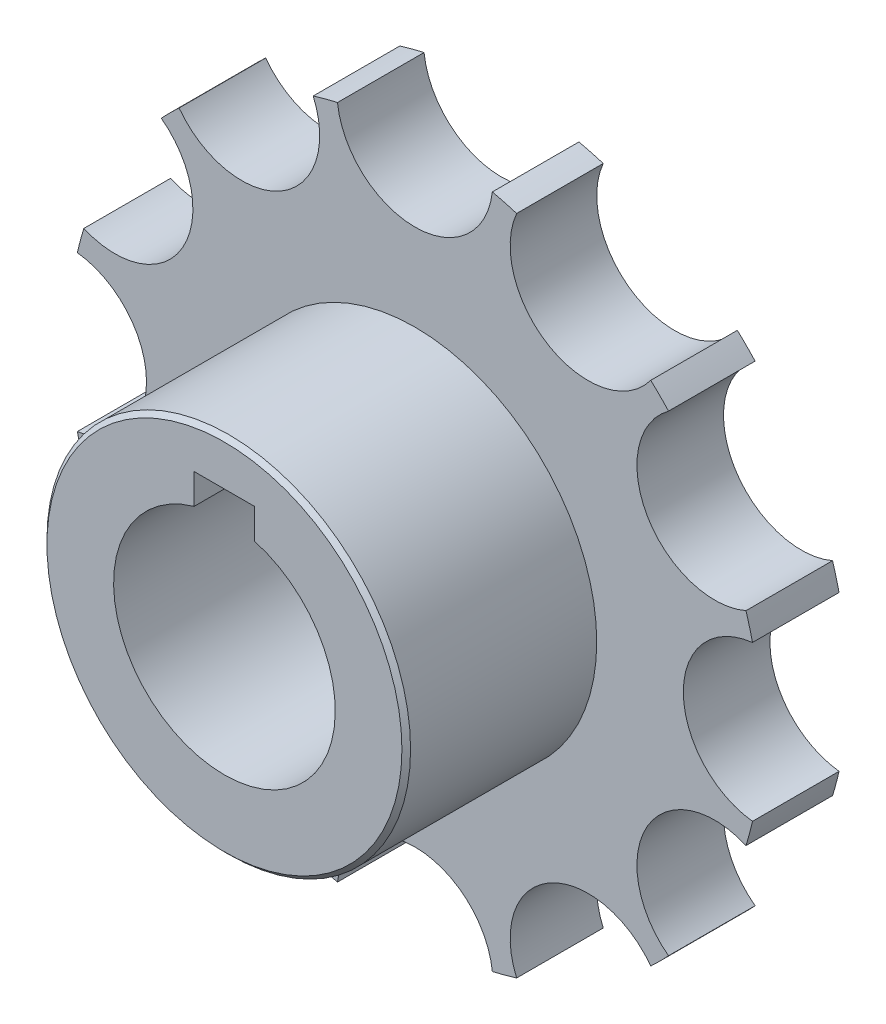
SolidWorks part; units mm, degrees
ref_plane "Přední rovina" through (0, 0, 0) normal (0, 0, 1) x (1, 0, 0)
ref_plane "Horní rovina" through (0, 0, 0) normal (0, 1, 0) x (1, 0, 0)
ref_plane "Pravá rovina" through (0, 0, 0) normal (1, 0, 0) x (0, 0, -1)
sketch "Skica1" plane through (0, 0, 0) normal (0, 0, 1) x (1, 0, 0)
  line L0 (-51.8674, 0) -> (69.1461, 0) construction
  line L1 (0, 65.5579) -> (0, -54.8107) construction
  line L3 (-3.5, 9.8) -> (3.5, 9.8)
  line L4 (-3.5, 9.8) -> (-3.5, 15.8)
  line L5 (-3.5, 15.8) -> (3.5, 15.8)
  line L6 (3.5, 9.8) -> (3.5, 15.8)
  line L7 (-3.5, 9.8) -> (3.5, 15.8) construction
  line L8 (-3.5, 15.8) -> (3.5, 9.8) construction
  circle A0 centre (0, 0) radius 12.8
  circle A1 centre (0, 0) radius 21
  circle A2 centre (0, 0) radius 40
  circle A3 centre (0, 40) radius 9
  circle A4 centre (20, 34.641) radius 9
  circle A5 centre (34.641, 20) radius 9
  circle A6 centre (40, 0) radius 9
  circle A7 centre (34.641, -20) radius 9
  circle A8 centre (20, -34.641) radius 9
  circle A9 centre (0, -40) radius 9
  circle A10 centre (-20, -34.641) radius 9
  circle A11 centre (-34.641, -20) radius 9
  circle A12 centre (-40, 0) radius 9
  circle A13 centre (-34.641, 20) radius 9
  circle A14 centre (-20, 34.641) radius 9
  point P7 (0, 12.8)
  point P41 (0, 0)
  dimension "D1" = 25.6
  dimension "D4" = 42
  dimension "D5" = 80
  dimension "D6" = 18
  dimension "D2" = 3
  dimension "D3" = 7
  dimension "D7" = 12
extrude "Přidat vysunutím2" add sketch "Skica1" along normal blind 10 contours A1 A0 L4 L5 L6 | A14 A2 A13 A12 A11 A10 A9 A8 A7 A6 A5 A4 A3 A1
sketch "Skica2" plane through (0, 0, 10) normal (0, 0, 1) x (1, 0, 0)
  circle A0 centre (0, 0) radius 21
  dimension "D1" = 42
extrude "Přidat vysunutím3" add sketch "Skica2" along normal blind 22
sketch "Skica3" plane through (0, 0, 0) normal (0, 0, -1) x (-1, 0, 0)
  line L0 (-3.5, 12.3122) -> (3.5, 12.3122)
  line L2 (-3.5, 12.3122) -> (-3.5, 15.8)
  line L3 (-3.5, 15.8) -> (3.5, 15.8)
  line L4 (3.5, 12.3122) -> (3.5, 15.8)
  line L5 (0, 12.8) -> (3.5, 15.8) construction
  line L6 (-3.5, 15.8) -> (0, 12.8) construction
  circle A0 centre (0, 0) radius 12.8
  point P3 (0, 12.8)
extrude "Odebrat vysunutím1" cut sketch "Skica3" against normal blind 61 contours L0 A0 | L0 A0 | A0 L3 L2 L0
chamfer "Zkosení3" distance 0.5 angle 45 1 edges at (21, 0, 32)
